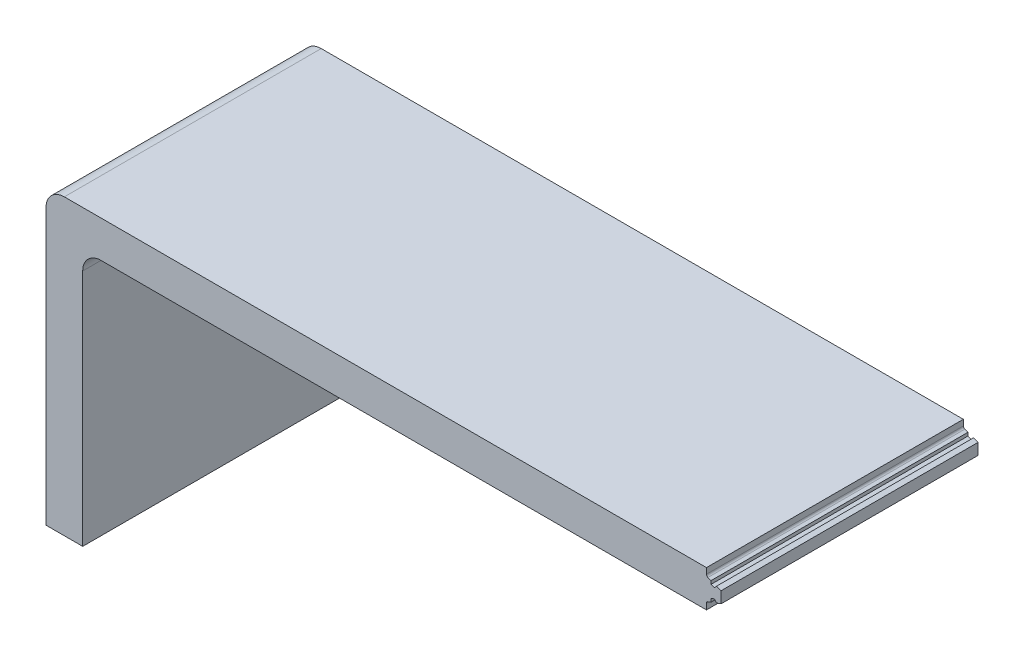
SolidWorks part; units mm, degrees
ref_plane "Front Plane" through (0, 0, 0) normal (0, 0, 1) x (1, 0, 0)
ref_plane "Top Plane" through (0, 0, 0) normal (0, 1, 0) x (1, 0, 0)
ref_plane "Right Plane" through (0, 0, 0) normal (1, 0, 0) x (0, 0, -1)
sketch "Sketch1" plane through (0, 0, 0) normal (0, 0, 1) x (1, 0, 0)
  line L0 (0, 0) -> (0, 101.6)
  line L6 (12.7, 88.9) -> (12.7, 0)
  line L7 (12.7, 0) -> (0, 0)
  line L8 (0, 101.6) -> (233.68, 101.6)
  line L10 (233.68, 88.9) -> (12.7, 88.9)
  line L14 (233.68, 88.9) -> (233.68, 101.6)
  dimension "D1" = 101.6
  dimension "D2" = 12.7
  dimension "D3" = 12.7
  dimension "D4" = 233.68
extrude "Boss-Extrude2" add sketch "Sketch1" along normal blind 88.9
sketch "Sketch8" plane through (0, 0, 88.9) normal (0, 0, 1) x (1, 0, 0)
  line L4 (233.68, 101.6) -> (0, 101.6) construction
  line L5 (228.6, 101.6) -> (233.68, 101.6)
  line L8 (228.6, 88.9) -> (233.68, 88.9)
  line L15 (233.68, 95.25) -> (228.6, 95.25) construction
  line L20 (232.1015, 97.7855) -> (231.3719, 96.916)
  line L21 (233.68, 88.9) -> (233.68, 101.6) construction
  line L28 (232.1015, 97.7855) -> (233.68, 97.211)
  line L29 (230.1785, 97.3503) -> (231.3719, 96.916)
  line L30 (230.1785, 98.4855) -> (230.1785, 97.3503)
  line L31 (228.6, 99.06) -> (230.1785, 98.4855)
  line L37 (228.6, 101.6) -> (228.6, 99.06)
  line L38 (233.68, 101.6) -> (233.68, 97.211)
  line L39 (228.6, 88.9) -> (228.6, 91.44)
  line L40 (228.6, 91.44) -> (230.1785, 92.0145)
  line L41 (230.1785, 92.0145) -> (230.1785, 93.1497)
  line L42 (230.1785, 93.1497) -> (231.3719, 93.584)
  line L43 (232.1015, 92.7145) -> (231.3719, 93.584)
  line L44 (232.1015, 92.7145) -> (233.68, 93.289)
  line L45 (233.68, 88.9) -> (233.68, 93.289)
  dimension "D1" = 5.08
extrude "Cut-Extrude3" cut sketch "Sketch8" against normal through all
fillet "Fillet2" radius 6.35 2 edges at (12.7, 88.9, 44.45) (0, 101.6, 44.45)
fillet "Fillet4" radius 0.762 2 edges at (228.6, 99.06, 44.45) (228.6, 91.44, 44.45)
